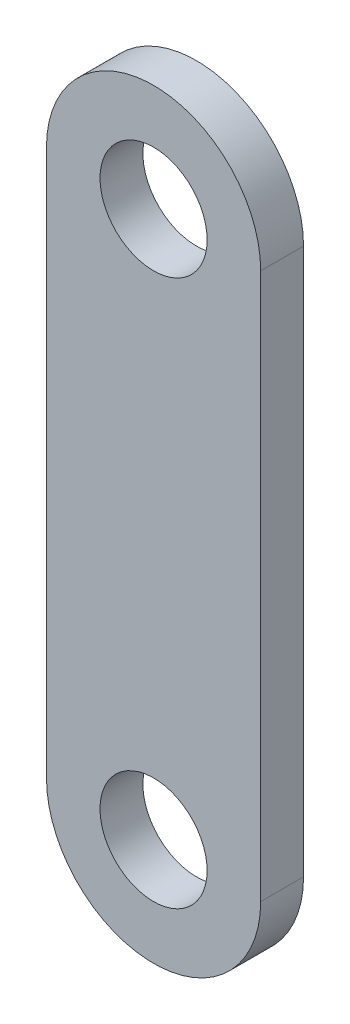
SolidWorks part; units mm, degrees
ref_plane "Front Plane" through (0, 0, 0) normal (0, 0, 1) x (1, 0, 0)
ref_plane "Top Plane" through (0, 0, 0) normal (0, 1, 0) x (1, 0, 0)
ref_plane "Right Plane" through (0, 0, 0) normal (1, 0, 0) x (0, 0, -1)
sketch "Sketch1" plane through (0, 0, 0) normal (0, 0, 1) x (1, 0, 0)
  line L1 (-50, 127.5) -> (-50, -127.5)
  line L2 (50, 127.5) -> (50, -127.5)
  circle A0 centre (0, 127.5) radius 25
  circle A1 centre (0, -127.5) radius 25
  arc A2 (50, 127.5) -> (-50, 127.5) centre (0, 127.5) ccw
  arc A3 (-50, -127.5) -> (50, -127.5) centre (0, -127.5) ccw
  point P4 (0, 0)
extrude "Boss-Extrude1" add sketch "Sketch1" along normal mid plane 20
